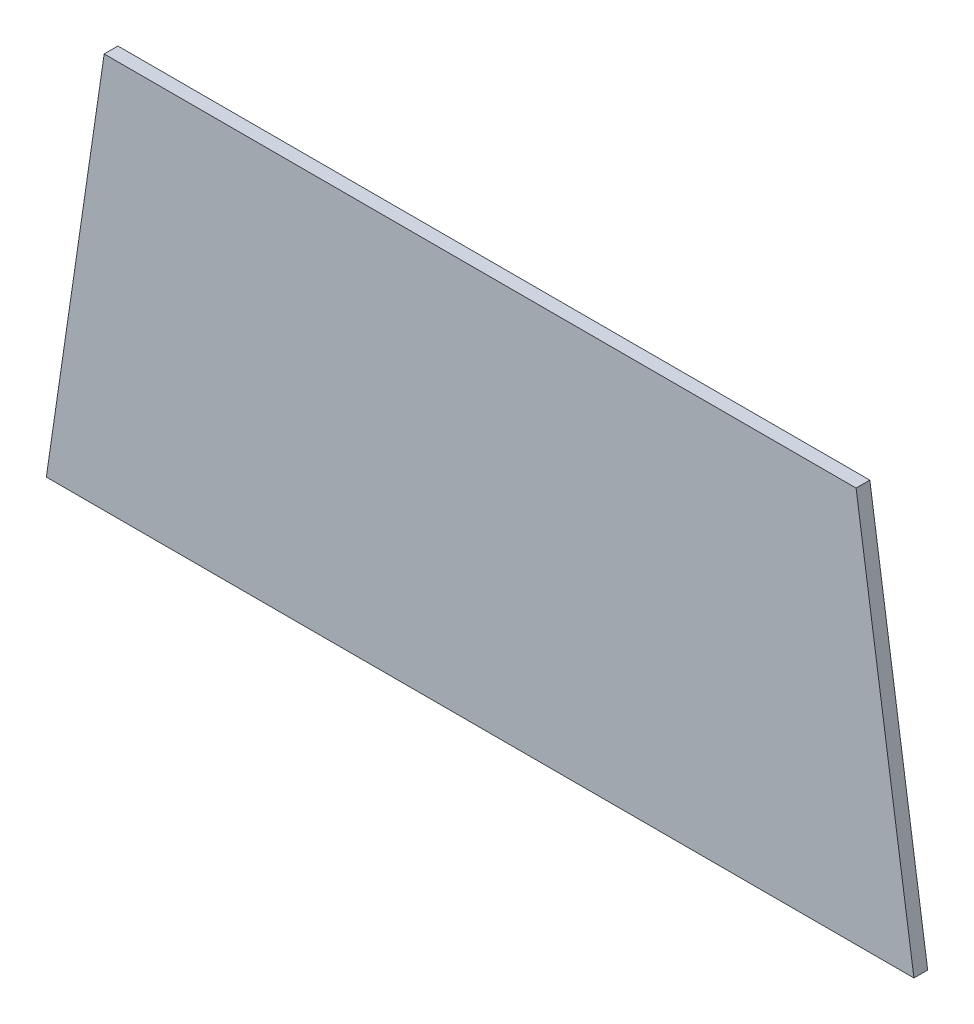
SolidWorks part; units mm, degrees
ref_plane "Front Plane" through (0, 0, 0) normal (0, 0, 1) x (1, 0, 0)
ref_plane "Top Plane" through (0, 0, 0) normal (0, 1, 0) x (1, 0, 0)
ref_plane "Right Plane" through (0, 0, 0) normal (1, 0, 0) x (0, 0, -1)
sketch "Sketch1" plane through (0, 0, 0) normal (0, 0, 1) x (1, 0, 0)
  line L0 (0, 0) -> (3.365, 23)
  line L1 (0, 0) -> (50.47, 0)
  line L3 (3.365, 23) -> (47.105, 23)
  line L5 (50.47, 0) -> (47.105, 23)
  dimension "D1" = 43.74
  dimension "D2" = 3.365
  dimension "D3" = 50.47
  dimension "D4" = 23
  dimension "D6" = 98.324
extrude "Boss-Extrude1" add sketch "Sketch1" along normal blind 0.8
